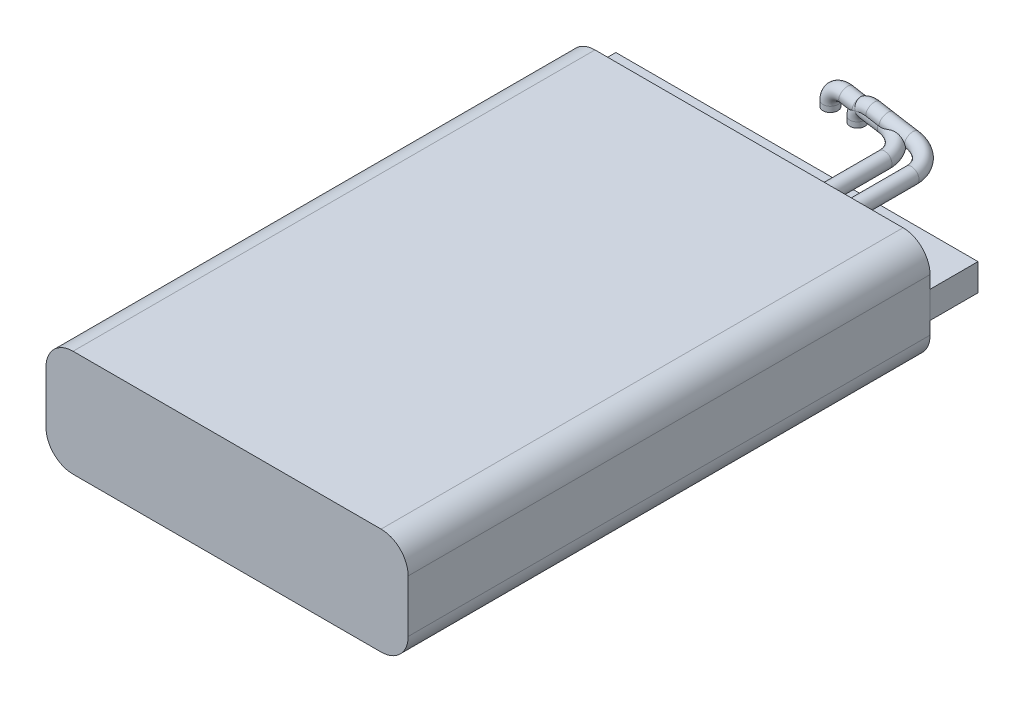
SolidWorks part; units mm, degrees
ref_plane "Front Plane" through (0, 0, 0) normal (0, 0, 1) x (1, 0, 0)
ref_plane "Top Plane" through (0, 0, 0) normal (0, 1, 0) x (1, 0, 0)
ref_plane "Right Plane" through (0, 0, 0) normal (1, 0, 0) x (0, 0, -1)
sketch "Sketch1" plane through (0, 0, 0) normal (0, 1, 0) x (1, 0, 0)
  line L1 (-17, 24.5) -> (17, 24.5)
  line L2 (-17, 24.5) -> (-17, -24.5)
  line L3 (-17, -24.5) -> (17, -24.5)
  line L4 (17, 24.5) -> (17, -24.5)
  point P4 (0, 24.5)
  point P5 (17, 0)
  dimension "D1" = 49
  dimension "D2" = 34
extrude "Boss-Extrude1" add sketch "Sketch1" along normal mid plane 10
fillet "Fillet1" radius 2.54 4 edges at (-17, -5, 0) (-17, 5, 0) (17, -5, 0) (17, 5, 0)
sketch "Sketch2" plane through (0, 0, 24.5) normal (0, 0, 1) x (1, 0, 0)
  line L1 (-17, 1.27) -> (17, 1.27)
  line L2 (-17, 1.27) -> (-17, -1.27)
  line L3 (-17, -1.27) -> (17, -1.27)
  line L4 (17, 1.27) -> (17, -1.27)
  line L5 (0, -6.443) -> (0, 6.443) construction
  line L6 (17, 2.46) -> (17, -2.46) construction
  point P4 (17, 0)
  point P6 (0, 1.27)
  dimension "D1" = 2.54
extrude "Boss-Extrude2" add sketch "Sketch2" along normal up to surface (4.5 mm away) from offset 53.5 separate body offset against normal yes
sketch3d "3DSketch1"
  line L0 (-2.54, 1.27, -34.682) -> (-2.54, 1.778, -34.682)
  line L1 (0.2015, 2.8078, -34.682) -> (-1.0491, 3.0286, -34.682)
  line L2 (5.08, 2.032, -32.142) -> (5.08, 2.032, -24.522)
  arc A0 (0.2015, 2.8078, -34.682) -> (2.5694, 2.4171, -34.682) centre (18.6768, 107.4208, -34.682) ccw
  arc A1 (2.5694, 2.4171, -34.682) -> (5.08, 2.032, -32.142) centre (2.5694, 2.4171, -32.142) ccw
  arc A2 (-2.54, 1.778, -34.682) -> (-1.0491, 3.0286, -34.682) centre (-1.27, 1.778, -34.682) ccw
  point P3 (18.6768, 107.4208, 71.5499)
  point P7 (2.1842, -0.0935, -32.142)
  point P9 (0, 0, 0)
  point P11 (-1.27, 1.778, -35.952)
  point P13 (0, 0, 0)
  point P14 (5.08, 6.016, -24.522)
  point P16 (5.08, 3.617, -24.522)
  point P17 (5.0892, 1.27, -24.5)
  point P18 (5.08, 2.1749, -24.522)
  dimension "D4" = 2.54
  dimension "D8" = 7.62
  dimension "D7" = 5.08
  dimension "D2" = 1.27
  dimension "D9" = 1.27
  dimension "D1" = 2.54
  dimension "D3" = 0.508
  dimension "D5" = 59.182
  dimension "D6" = 2.032
sweep "Sweep2" add path "3DSketch1" circular profile diameter 1.397 parameters "D3"=1.397
move or copy body "Body-Move/Copy1" bodies to move or copy 104 copy yes number of copies 1 translate (2.54, 0, 0) parameters "D1"=2.54, "D2"=0, "D3"=0
